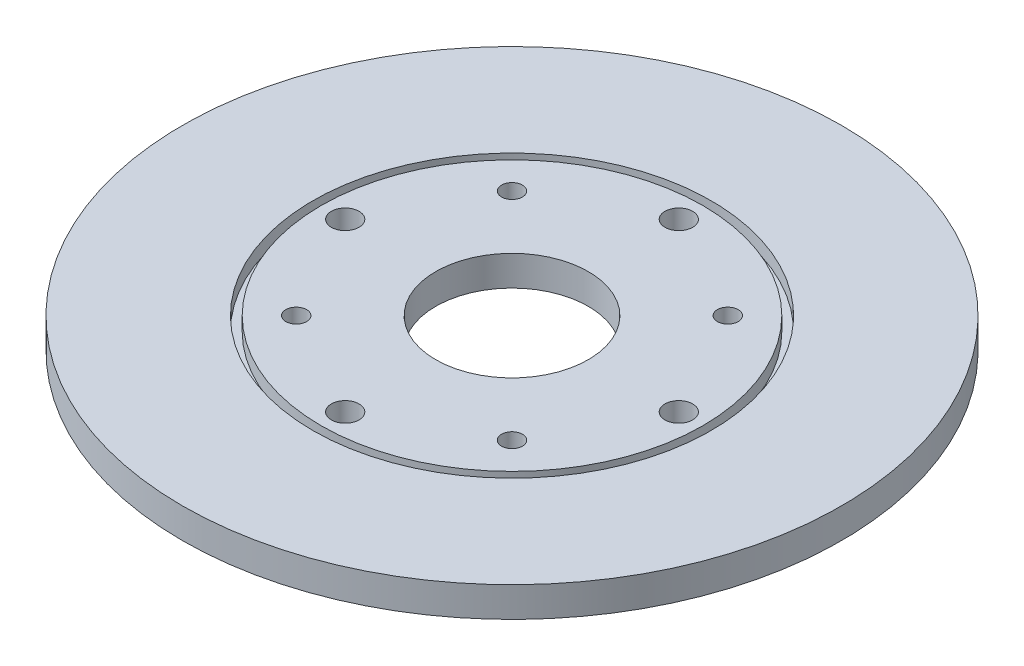
SolidWorks part; units mm, degrees
ref_plane "Front" through (0, 0, 0) normal (0, 0, 1) x (1, 0, 0)
ref_plane "Top" through (0, 0, 0) normal (0, 1, 0) x (1, 0, 0)
ref_plane "Right" through (0, 0, 0) normal (1, 0, 0) x (0, 0, -1)
sketch "Sketch1" plane through (0, 0, 0) normal (0, 1, 0) x (1, 0, 0)
  line L1 (-15.55, -15.55) -> (15.55, -15.55) construction
  line L2 (-15.55, -15.55) -> (-15.55, 15.55) construction
  line L3 (-15.55, 15.55) -> (15.55, 15.55) construction
  line L4 (15.55, -15.55) -> (15.55, 15.55) construction
  line L5 (-15.55, -15.55) -> (15.55, 15.55) construction
  line L6 (-15.55, 15.55) -> (15.55, -15.55) construction
  circle A0 centre (0, 0) radius 47.5
  circle A1 centre (0, 0) radius 11
  circle A2 centre (15.55, 15.55) radius 1.5
  circle A3 centre (15.55, -15.55) radius 1.5
  circle A4 centre (-15.55, -15.55) radius 1.5
  circle A5 centre (-15.55, 15.55) radius 1.5
  dimension "D1" = 3
  dimension "D2" = 95
  dimension "D3" = 22
  dimension "D4" = 31.1
extrude "Boss-Extrude1" add sketch "Sketch1" along normal blind 4.34
sketch "Sketch2" plane through (0, 4.34, 0) normal (0, 1, 0) x (1, 0, 0)
  circle A0 centre (0, 0) radius 27.5
  circle A1 centre (0, 0) radius 28.7
  dimension "D1" = 1.2
  dimension "D2" = 55
extrude "Cut-Extrude1" cut sketch "Sketch2" against normal blind 2
sketch "Sketch3" plane through (0, 4.34, 0) normal (0, 1, 0) x (1, 0, 0)
  line L0 (0, 24.0416) -> (24.0416, 0) construction
  line L1 (0, 24.0416) -> (-24.0416, 0) construction
  line L2 (24.0416, 0) -> (0, -24.0416) construction
  line L3 (-24.0416, 0) -> (0, -24.0416) construction
  line L4 (0, 24.0416) -> (0, -24.0416) construction
  line L5 (24.0416, 0) -> (-24.0416, 0) construction
  line L6 (15.55, -15.55) -> (0, 0) construction
  circle A0 centre (24.0416, 0) radius 2
  circle A1 centre (0, -24.0416) radius 2
  circle A2 centre (-24.0416, 0) radius 2
  circle A3 centre (0, 24.0416) radius 2
  point P1 (0, 0)
  dimension "D1" = 4
  dimension "D2" = 34
extrude "Cut-Extrude2" cut sketch "Sketch3" against normal up to next contours A2
sketch "Sketch4" plane through (0, 0, 0) normal (0, -1, 0) x (1, 0, 0)
  circle A0 centre (0, 0) radius 30.7
  circle A1 centre (0, 0) radius 29.5
  dimension "D1" = 1.2
  dimension "D2" = 59
